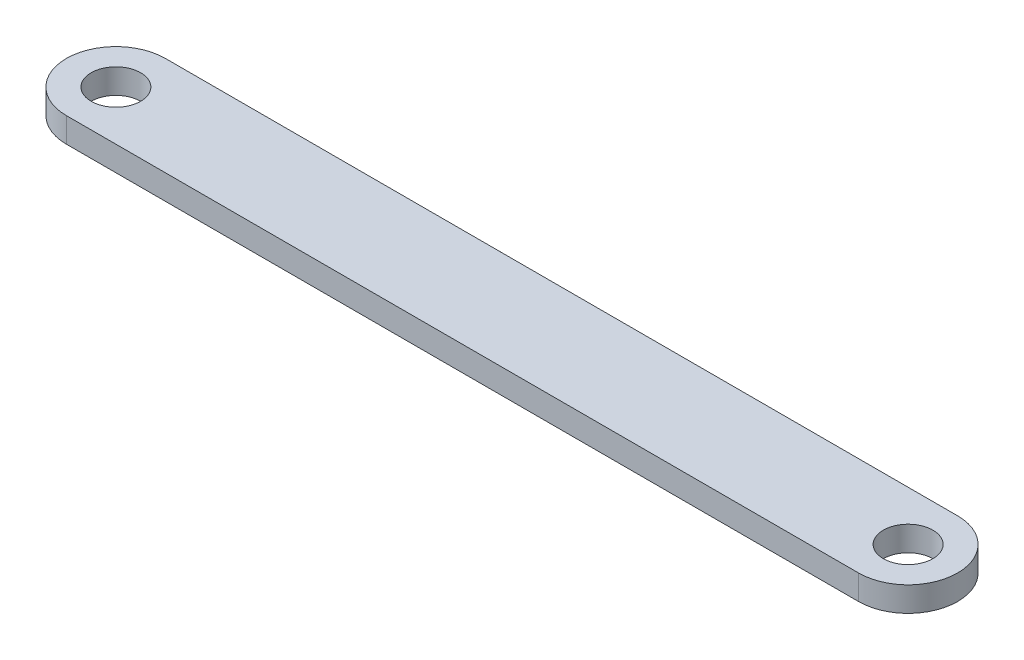
SolidWorks part; units mm, degrees
ref_plane "Front Plane" through (0, 0, 0) normal (0, 0, 1) x (1, 0, 0)
ref_plane "Top Plane" through (0, 0, 0) normal (0, 1, 0) x (1, 0, 0)
ref_plane "Right Plane" through (0, 0, 0) normal (1, 0, 0) x (0, 0, -1)
sketch "Sketch1" plane through (0, 0, 0) normal (0, 1, 0) x (1, 0, 0)
  line L0 (-80, 0) -> (80, 0) construction
  line L1 (-80, 10) -> (80, 10)
  line L2 (-80, -10) -> (80, -10)
  arc A0 (-80, 10) -> (-80, -10) centre (-80, 0) ccw
  arc A1 (80, -10) -> (80, 10) centre (80, 0) ccw
  circle A2 centre (-80, 0) radius 5
  circle A3 centre (80, 0) radius 5
  point P2 (0, 0)
  dimension "D3" = 10
  dimension "D1" = 160
  dimension "D2" = 20
extrude "Boss-Extrude1" add sketch "Sketch1" along normal blind 5
